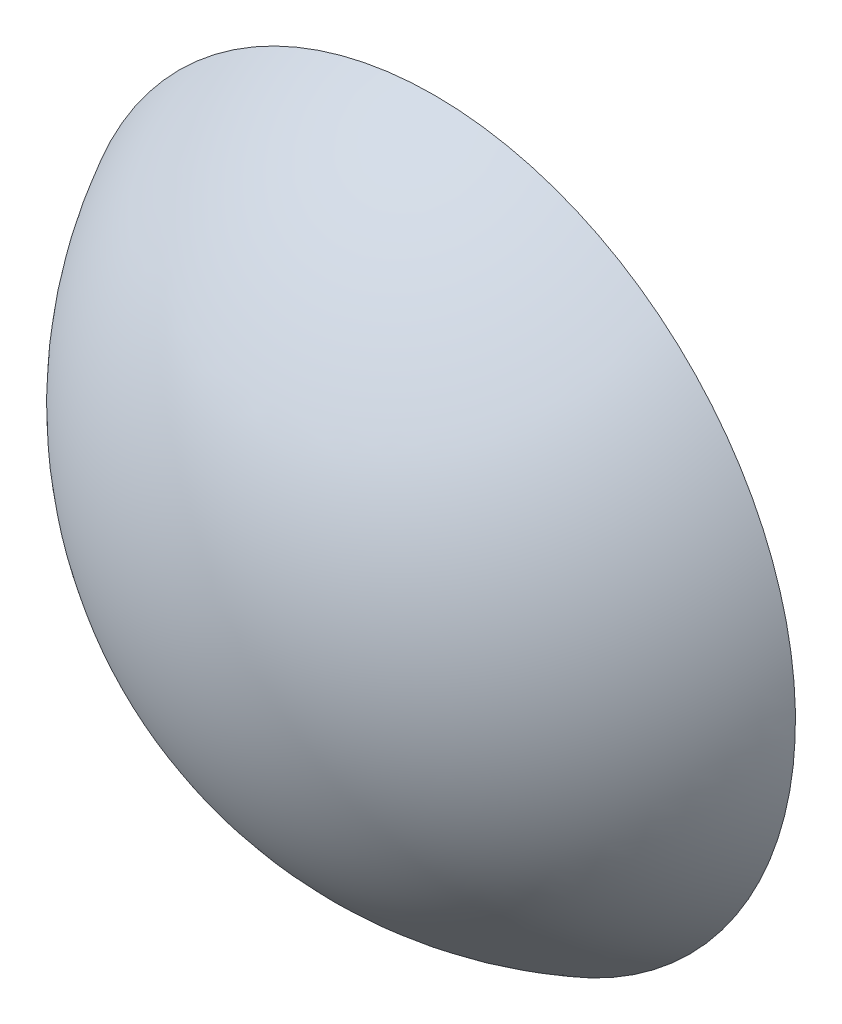
SolidWorks part; units mm, degrees
ref_plane "Front Plane" through (0, 0, 0) normal (1, 0, 0) x (0, 1, 0)
ref_plane "Top Plane" through (0, 0, 0) normal (0, 0, 1) x (0, 1, 0)
ref_plane "Right Plane" through (0, 0, 0) normal (0, 1, 0) x (-1, 0, 0)
sketch "Sketch1" plane through (0, 0, 0) normal (1, 0, 0) x (0, 1, 0)
  line L0 (0, 4.3819) -> (8.4572, 4.3819)
  line L1 (0, 4.3819) -> (0, 9.525)
  arc A0 (8.4572, 4.3819) -> (0, 9.525) centre (0, 0) ccw
  dimension "D1" = 19.05
revolve "Revolve1" add sketch "Sketch1" angle 360 about L1
